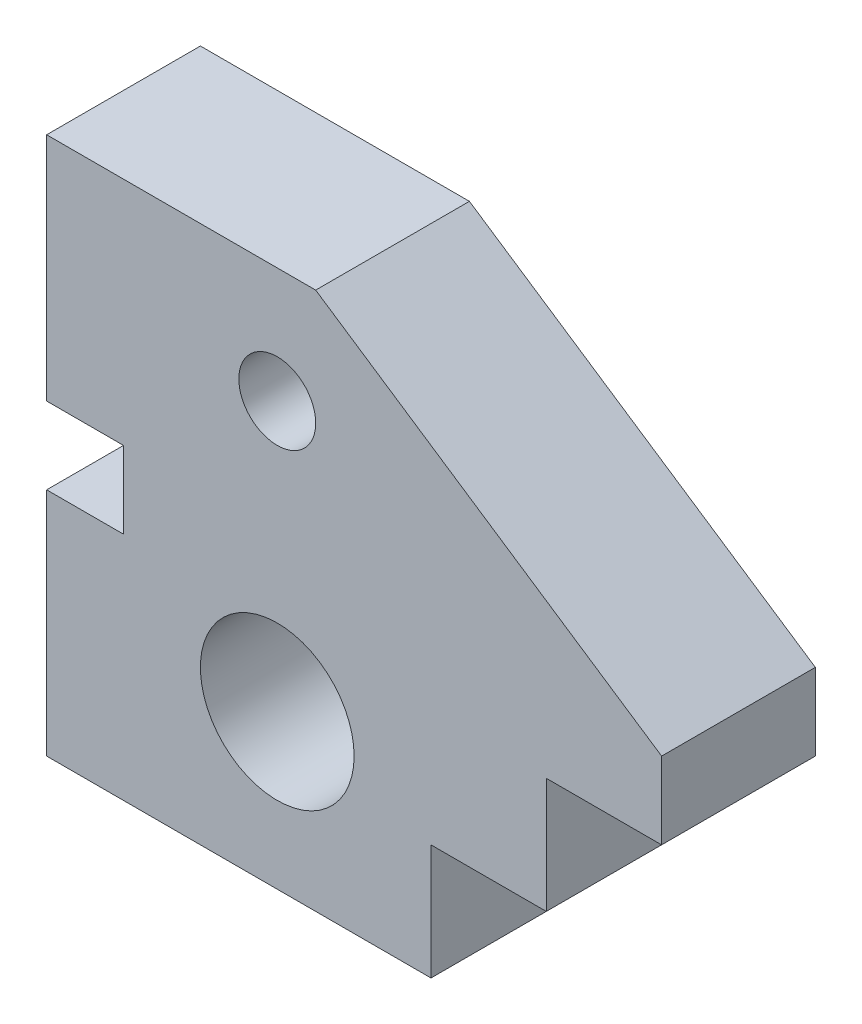
SolidWorks part; units mm, degrees
ref_plane "Front Plane" through (0, 0, 0) normal (0, 0, 1) x (1, 0, 0)
ref_plane "Top Plane" through (0, 0, 0) normal (0, 1, 0) x (1, 0, 0)
ref_plane "Right Plane" through (0, 0, 0) normal (1, 0, 0) x (0, 0, -1)
sketch "Sketch1" plane through (0, 0, 0) normal (0, 0, 1) x (1, 0, 0)
  line L0 (-28.577, 0.1312) -> (-28.577, 0)
  line L1 (-28.577, -21.8434) -> (21.423, -21.8434)
  line L2 (21.423, -21.8434) -> (21.423, -6.8434)
  line L3 (21.423, -6.8434) -> (36.423, -6.8434)
  line L4 (36.423, -6.8434) -> (36.423, 8.1566)
  line L5 (36.423, 8.1566) -> (51.423, 8.1566)
  line L6 (51.423, 8.1566) -> (51.423, 18.1566)
  line L7 (51.423, 18.1566) -> (6.423, 48.1566)
  line L8 (6.423, 48.1566) -> (-28.577, 48.1566)
  line L9 (-28.577, 48.1566) -> (-28.577, 18.1566)
  line L10 (-28.577, 18.1566) -> (-18.577, 18.1566)
  line L11 (-18.577, 18.1566) -> (-18.577, 8.1566)
  line L12 (-18.577, 8.1566) -> (-28.577, 8.1566)
  line L13 (-28.577, 0.1312) -> (-28.577, 0)
  line L14 (-28.577, 8.1566) -> (-28.577, -21.8434)
  circle A0 centre (1.423, -1.8434) radius 10
  circle A1 centre (1.423, 33.1566) radius 5
  dimension "D1" = 10
  dimension "D2" = 20
  dimension "D3" = 15
  dimension "D4" = 20
  dimension "D5" = 30
  dimension "D6" = 15
  dimension "D7" = 30
  dimension "D8" = 10
  dimension "D9" = 35
  dimension "D10" = 50
  dimension "D11" = 70
  dimension "D12" = 15
  dimension "D13" = 40
  dimension "D14" = 80
  dimension "D15" = 10
  dimension "D16" = 65
other "AlignGroup1"
other "AlignGroup2"
extrude "Boss-Extrude3" add sketch "Sketch1" along normal blind 20 contours L12 L14 L0 L1 L2 L3 L4 L5 L6 L7 L8 L9 L10 L11 A1 A0
